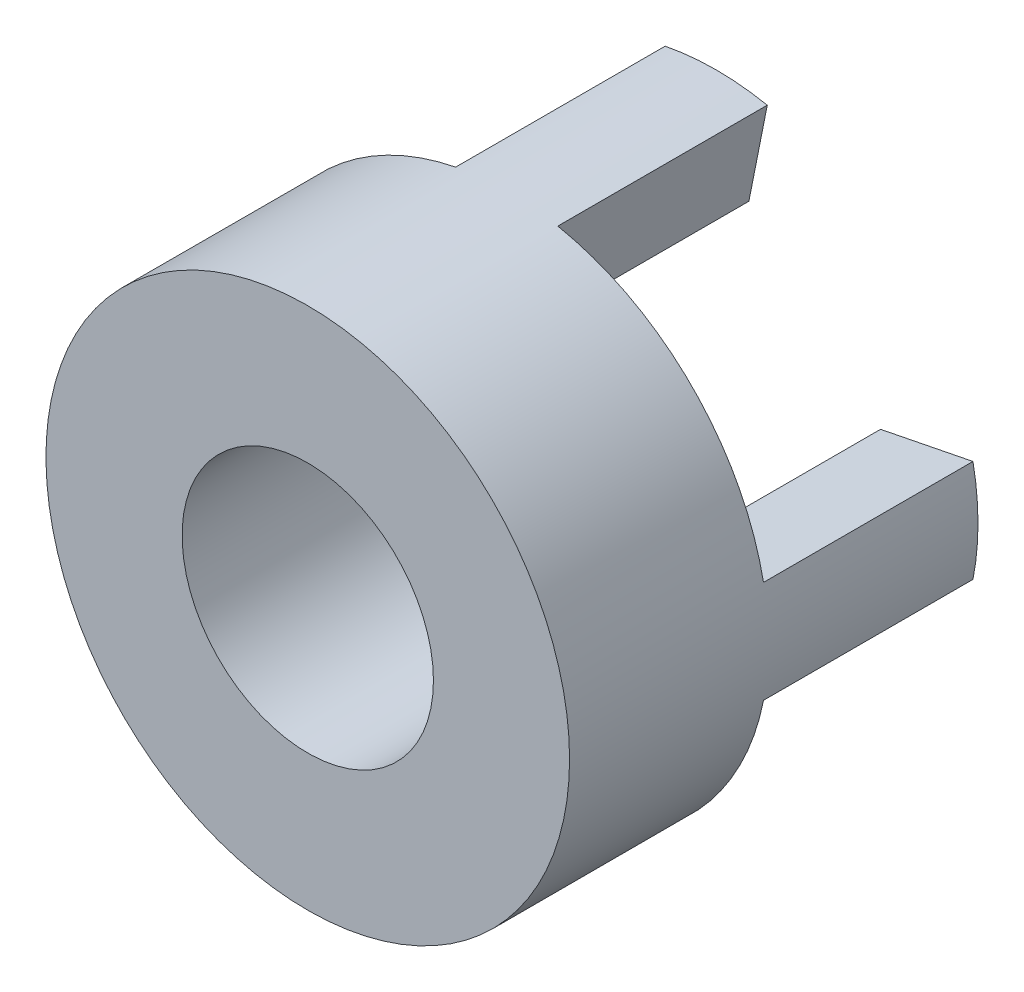
SolidWorks part; units mm, degrees
ref_plane "前视基准面" through (0, 0, 0) normal (0, 0, 1) x (1, 0, 0)
ref_plane "上视基准面" through (0, 0, 0) normal (0, 1, 0) x (1, 0, 0)
ref_plane "右视基准面" through (0, 0, 0) normal (1, 0, 0) x (0, 0, -1)
sketch "草图1" plane through (0, 0, 0) normal (0, 0, 1) x (1, 0, 0)
  circle A0 centre (0, 0) radius 6
  circle A1 centre (0, 0) radius 12.5
  dimension "D1" = 25
  dimension "D2" = 12
extrude "凸台-拉伸1" add sketch "草图1" along normal blind 9.5
sketch "草图2" plane through (0, 0, 0) normal (0, 0, -1) x (-1, 0, 0)
  line L0 (0, 15.8669) -> (0, -17.8879) construction
  line L1 (7.8463, -1.5607) -> (12.2598, -2.4386)
  line L2 (-3.1318, 15.7447) -> (3.1318, -15.7447) construction
  line L3 (3.1318, 15.7447) -> (-3.1318, -15.7447) construction
  line L14 (1.5607, 7.8463) -> (2.4386, 12.2598)
  line L15 (-2.4386, 12.2598) -> (-1.5607, 7.8463)
  line L20 (12.2598, 2.4386) -> (7.8463, 1.5607)
  line L21 (-1.5607, -7.8463) -> (-2.4386, -12.2598)
  line L22 (2.4386, -12.2598) -> (1.5607, -7.8463)
  line L23 (-7.8463, 1.5607) -> (-12.2598, 2.4386)
  line L24 (-12.2598, -2.4386) -> (-7.8463, -1.5607)
  line L25 (0, 0) -> (1.5607, 7.8463) construction
  arc A8 (2.4386, 12.2598) -> (-2.4386, 12.2598) centre (0, 0) ccw
  arc A9 (1.5607, 7.8463) -> (-1.5607, 7.8463) centre (0, 0) ccw
  arc A16 (12.2598, -2.4386) -> (12.2598, 2.4386) centre (0, 0) ccw
  arc A17 (7.8463, -1.5607) -> (7.8463, 1.5607) centre (0, 0) ccw
  arc A18 (-2.4386, -12.2598) -> (2.4386, -12.2598) centre (0, 0) ccw
  arc A19 (-1.5607, -7.8463) -> (1.5607, -7.8463) centre (0, 0) ccw
  arc A20 (-12.2598, 2.4386) -> (-12.2598, -2.4386) centre (0, 0) ccw
  arc A21 (-7.8463, 1.5607) -> (-7.8463, -1.5607) centre (0, 0) ccw
  dimension "D2" = 12.5
  dimension "D3" = 8
  dimension "D1" = 11.25
  dimension "D4" = 4
extrude "凸台-拉伸2" add sketch "草图2" along normal blind 10
